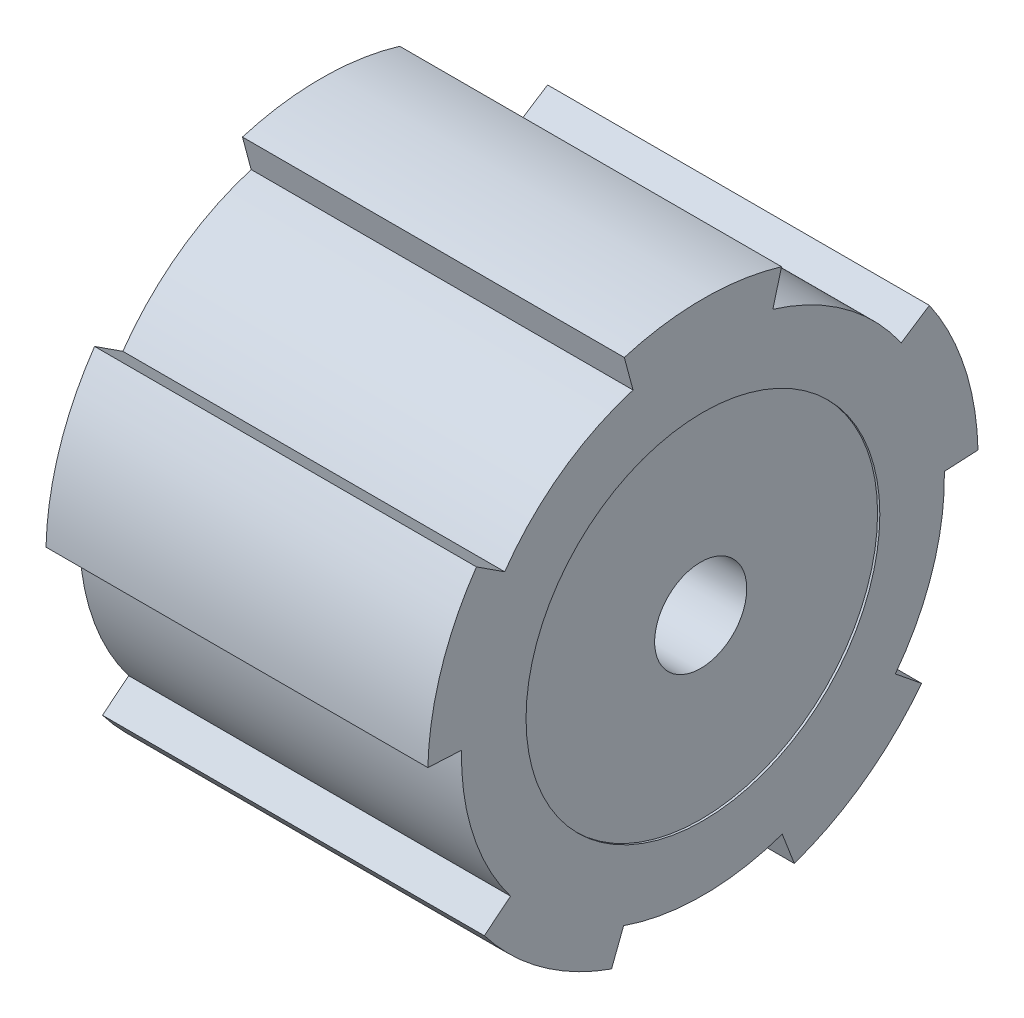
SolidWorks part; units mm, degrees
ref_plane "Front Plane" through (0, 0, 0) normal (0, 0, 1) x (1, 0, 0)
ref_plane "Top Plane" through (0, 0, 0) normal (0, 1, 0) x (1, 0, 0)
ref_plane "Right Plane" through (0, 0, 0) normal (1, 0, 0) x (0, 0, -1)
sketch "Sketch2" plane through (0, 0, 0) normal (1, 0, 0) x (0, 0, -1)
  circle A0 centre (0, 0) radius 21.05 construction
  circle A1 centre (0, 0) radius 4 construction
  circle A2 centre (0, 0) radius 30.5 construction
  dimension "D1" = 42.1
  dimension "D2" = 8
  dimension "D3" = 61
sketch "Sketch4" plane through (0, 0, 0) normal (1, 0, 0) x (0, 0, -1)
  circle A0 centre (0, 0) radius 21.5
  dimension "D1" = 43
extrude "Boss-Extrude1" add sketch "Sketch4" against normal blind 34
sketch "Sketch5" plane through (0, 0, 0) normal (1, 0, 0) x (0, 0, -1)
  line L0 (-6.2235, 20.5795) -> (-7, 23.4773)
  line L1 (6.2235, 20.5795) -> (7, 23.4773)
  line L2 (0, 0) -> (0, 21.5) construction
  line L3 (-6.2235, 20.5795) -> (6.2235, 20.5795) construction
  line L4 (0, 21.5) -> (0, 24.4987) construction
  circle A0 centre (0, 0) radius 21.5 construction
  arc A1 (-6.2235, 20.5795) -> (6.2235, 20.5795) centre (0, 0) cw
  arc A2 (-7, 23.4773) -> (7, 23.4773) centre (0, 0) cw
  dimension "D3" = 14
  dimension "D1" = 3
  dimension "D2" = 105
extrude "Boss-Extrude2" add sketch "Sketch5" against normal up to surface (34 mm away) up to face at (-34, 0, -21.5)
pattern_circular "CirPattern1" count 5 over 360 about axis through (0, 0, 0) along (1, 0, 0) of "Boss-Extrude2"
sketch "Sketch6" plane through (0, 0, 0) normal (1, 0, 0) x (0, 0, -1)
  circle A0 centre (0, 0) radius 4.05
  dimension "D1" = 8.1
extrude "LongShaft" [suppressed] add sketch "Sketch6" along normal blind 23
sketch "Sketch7" plane through (-34, 0, 0) normal (-1, 0, 0) x (0, 0, 1)
  circle A0 centre (0, 0) radius 10
  dimension "D1" = 20
extrude "ShortShaft Key1" cut sketch "Sketch7" against normal blind 16
sketch "Sketch8" plane through (-34, 0, 0) normal (-1, 0, 0) x (0, 0, 1)
  line L0 (-7.9417, 6.077) -> (-9.8845, 7.6503)
  line L1 (-3.3255, 9.4309) -> (-4.2214, 11.7648)
  line L2 (-20.1651, 13.9123) -> (-7, 23.4773) construction
  line L3 (0, 0) -> (-13.5826, 18.6948) construction
  line L4 (-7.9417, 6.077) -> (-3.3255, 9.4309) construction
  arc A0 (-7.9417, 6.077) -> (-3.3255, 9.4309) centre (0, 0) cw
  circle A1 centre (0, 0) radius 10 construction
  arc A2 (-9.8845, 7.6503) -> (-4.2214, 11.7648) centre (0, 0) cw
  circle A4 centre (0, 0) radius 10 construction
  point P10 (-7.3469, 10.1121)
  point P17 (-5.6336, 7.7539)
  dimension "D1" = 7
  dimension "D2" = 105
  dimension "D3" = 2.5
extrude "ShortShaft Key2" cut sketch "Sketch8" against normal blind 16
pattern_circular "ShortShaft Key Patt" count 5 over 360 about axis through (0, 0, 0) along (1, 0, 0) of "ShortShaft Key2"
sketch "Sketch9" [suppressed] plane through (0, 0, 0) normal (1, 0, 0) x (0, 0, -1)
  circle A0 centre (0, 0) radius 13.5
  dimension "D1" = 27
extrude "Boss-Extrude4" [suppressed] add sketch "Sketch9" along normal blind 17
fillet "Fillet1" [suppressed] radius 2
sketch "Sketch10" plane through (0, 0, 0) normal (1, 0, 0) x (0, 0, -1)
  circle A0 centre (0, 0) radius 15.75
  dimension "D1" = 31.5
extrude "PulleyIndentation" cut sketch "Sketch10" against normal blind 0.2
sketch "Sketch11" plane through (0, 0, 0) normal (1, 0, 0) x (0, 0, -1)
  circle A1 centre (0, 0) radius 4.1
  dimension "D1" = 8.2
extrude "Metal Shaft Hole" cut sketch "Sketch11" against normal blind 14.5
